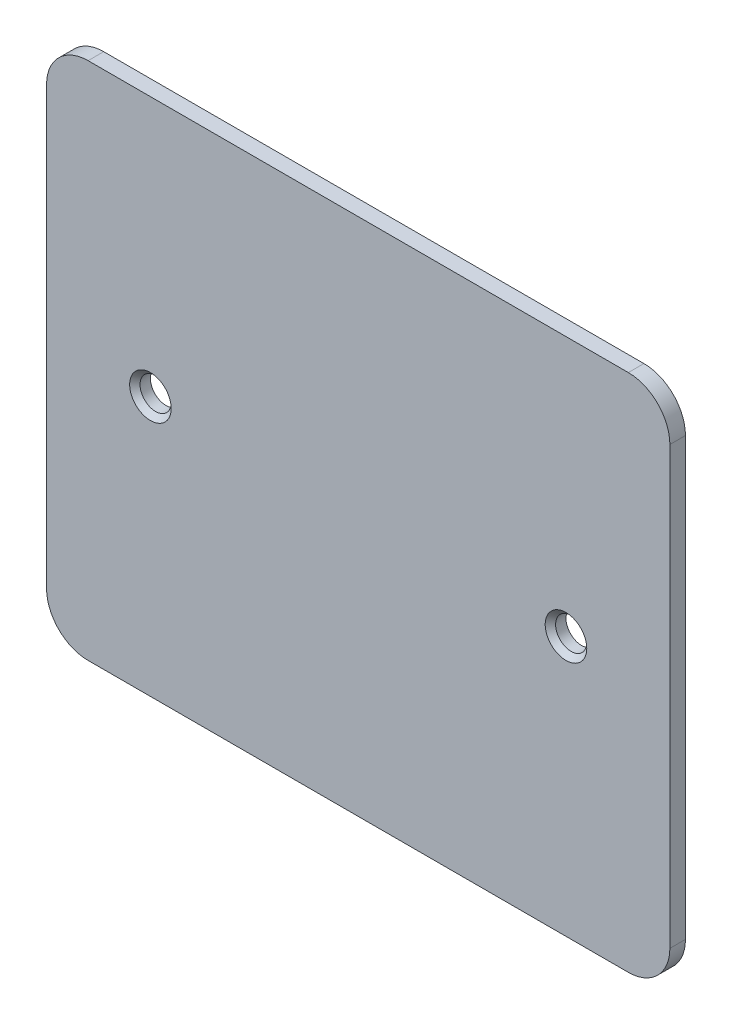
SolidWorks part; units mm, degrees
ref_plane "Plan de face" through (0, 0, 0) normal (0, 0, 1) x (1, 0, 0)
ref_plane "Plan de dessus" through (0, 0, 0) normal (0, 1, 0) x (1, 0, 0)
ref_plane "Plan de droite" through (0, 0, 0) normal (1, 0, 0) x (0, 0, -1)
sketch "Esquisse1" plane through (0, 0, 0) normal (0, 0, 1) x (1, 0, 0)
  line L0 (-60, 25) -> (-50, 25) construction
  line L1 (0, 0) -> (-60, 0)
  line L2 (0, 0) -> (0, 50)
  line L3 (0, 50) -> (-60, 50)
  line L4 (-60, 0) -> (-60, 50)
  line L5 (-50, 25) -> (-10, 25) construction
  line L6 (-10, 25) -> (0, 25) construction
  circle A0 centre (-50, 25) radius 1.5
  circle A1 centre (-10, 25) radius 1.5
  dimension "D5" = 3
  dimension "D1" = 60
  dimension "D2" = 50
  dimension "D3" = 10
  dimension "D4" = 10
extrude "Extrusion1" add sketch "Esquisse1" along normal blind 1.5
chamfer "Chanfrein1" distance 0.5 angle 45 2 edges at (-48.5, 25, 1.5) (-8.5, 25, 1.5)
fillet "Congé1" radius 4 4 edges at (0, 0, 0.75) (-60, 0, 0.75) (-60, 50, 0.75) (0, 50, 0.75)
